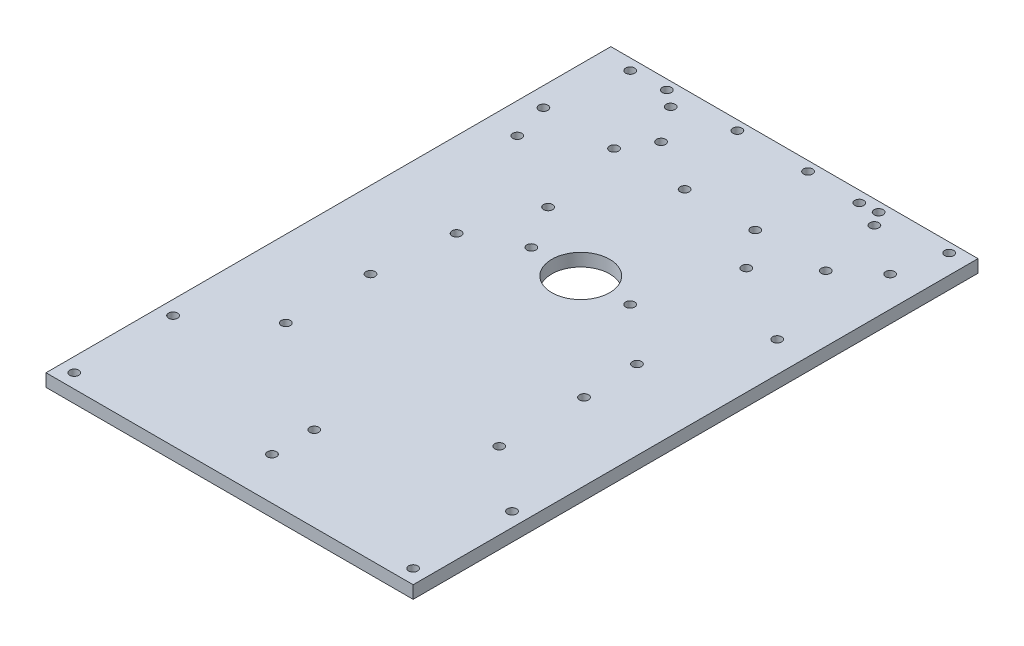
SolidWorks part; units mm, degrees
ref_plane "Front Plane" through (0, 0, 0) normal (0, 0, 1) x (1, 0, 0)
ref_plane "Top Plane" through (0, 0, 0) normal (0, 1, 0) x (1, 0, 0)
ref_plane "Right Plane" through (0, 0, 0) normal (1, 0, 0) x (0, 0, -1)
sketch "Sketch1" plane through (0, 0, 0) normal (0, 1, 0) x (1, 0, 0)
  line L0 (0, -55) -> (0, 55) construction
  line L5 (-65, -100) -> (65, -100)
  line L6 (-65, -100) -> (-65, 100)
  line L7 (-65, 100) -> (65, 100)
  line L8 (65, -100) -> (65, 100)
  line L9 (-65, -100) -> (65, 100) construction
  line L10 (-65, 100) -> (65, -100) construction
  line L11 (0, 100) -> (0, -100) construction
  line L12 (-100, -100) -> (100, -100) construction
  line L13 (-100, -100) -> (-100, 100) construction
  line L14 (-100, 100) -> (100, 100) construction
  line L15 (100, -100) -> (100, 100) construction
  line L16 (-100, -100) -> (100, 100) construction
  line L17 (-100, 100) -> (100, -100) construction
  point P0 (0, 0)
  point P1 (0, 0)
  point P6 (0, 0)
  dimension "D1" = 200
  dimension "D2" = 200
  dimension "D3" = 200
  dimension "D4" = 130
extrude "Boss-Extrude1" add sketch "Sketch1" along normal blind 4.5
sketch "Sketch3" plane through (0, 0, 0) normal (0, 1, 0) x (1, 0, 0)
  line L0 (-65, -90) -> (-55, -100) construction
  line L1 (-65, -100) -> (-55, -100) construction
  line L2 (-65, -100) -> (-65, -90) construction
  line L3 (-65, -90) -> (-55, -90) construction
  line L4 (-55, -100) -> (-55, -90) construction
  line L5 (-55, -90) -> (-65, -100) construction
  line L6 (0, -55) -> (0, 55) construction
  line L7 (65, -100) -> (55, -100) construction
  line L8 (65, -100) -> (65, -90) construction
  line L9 (65, -90) -> (55, -100) construction
  line L10 (65, -90) -> (55, -90) construction
  line L11 (55, -90) -> (65, -100) construction
  line L12 (55, -100) -> (55, -90) construction
  line L13 (-65, 100) -> (-65, -100) construction
  line L14 (-65, -65) -> (-55, -65) construction
  line L15 (-65, -65) -> (-65, -55) construction
  line L16 (-65, -55) -> (-55, -55) construction
  line L17 (-55, -65) -> (-55, -55) construction
  line L18 (-55, -55) -> (-65, -65) construction
  line L19 (-65, -65) -> (-55, -65) construction
  line L20 (-55, -65) -> (-65, -55) construction
  line L21 (55, -65) -> (65, -55) construction
  line L22 (65, -65) -> (55, -65) construction
  line L23 (55, -55) -> (65, -65) construction
  line L24 (55, -65) -> (55, -55) construction
  line L25 (65, -65) -> (65, -55) construction
  line L26 (65, -65) -> (55, -65) construction
  line L27 (65, -55) -> (55, -55) construction
  circle A0 centre (-60, -95) radius 1.6
  circle A1 centre (60, -95) radius 1.6
  circle A2 centre (-60, -60) radius 1.6
  circle A3 centre (60, -60) radius 1.6
  dimension "D3" = 3.2
  dimension "D7" = 3.2
  dimension "D1" = 10
  dimension "D2" = 10
  dimension "D4" = 10
  dimension "D5" = 10
  dimension "D6" = 25
extrude "Cut-Extrude1" cut sketch "Sketch3" along normal up to surface (4.5 mm away) up to face at (0, 4.5, 0)
sketch "Sketch4" plane through (0, 0, 0) normal (0, 1, 0) x (1, 0, 0)
  line L0 (42.545, 100) -> (-42.545, 100) construction
  line L1 (42.545, 100) -> (42.545, 1.702) construction
  line L2 (42.545, 1.702) -> (-42.545, 1.702) construction
  line L3 (-42.545, 100) -> (-42.545, 1.702) construction
  line L4 (42.545, 100) -> (-42.545, 1.702) construction
  line L5 (42.545, 1.702) -> (-42.545, 100) construction
  line L6 (0, 100) -> (0, 1.702) construction
  line L8 (0, -2.475) -> (0, 2.475) construction
  line L10 (42.545, 50.851) -> (-42.545, 50.851) construction
  line L12 (65, 100) -> (-65, 100) construction
  line L14 (65, -100) -> (65, 100)
  line L15 (65, 100) -> (-65, 100)
  line L16 (-65, 100) -> (-65, -100)
  line L17 (-65, -100) -> (65, -100)
  line L18 (65, -100) -> (65, 100)
  line L19 (65, 100) -> (-65, 100)
  line L20 (-65, 100) -> (-65, -100)
  line L21 (-65, -100) -> (65, -100)
  circle A0 centre (36.957, 7.29) radius 1.6
  circle A2 centre (-35.945, 92.13) radius 1.6
  circle A3 centre (36.445, 91.87) radius 1.6
  circle A4 centre (-35.055, 15.432) radius 1.6
  point P0 (0, 50.851)
  point P25 (0, 0)
  dimension "D3" = 0
  dimension "D4" = 3.2
  dimension "D5" = 13.73
  dimension "D1" = 85.09
  dimension "D2" = 98.298
  dimension "D6" = 5.588
  dimension "D7" = 5.588
  dimension "D8" = 6.1
  dimension "D9" = 8.13
  dimension "D10" = 7.87
  dimension "D11" = 6.6
  dimension "D12" = 98.298
  dimension "D13" = 85.09
  dimension "D14" = 7.49
extrude "Cut-Extrude2" cut sketch "Sketch4" along normal up to surface (4.5 mm away) contours A4 | A0 | A3 | A2 up to face at (60, 4.5, 93.4)
sketch "Sketch5" plane through (0, 0, 0) normal (0, 1, 0) x (1, 0, 0)
  line L5 (32.8, -52.298) -> (32.8, -2.298) construction
  line L8 (42.8, -2.298) -> (42.8, -52.298) construction
  line L12 (-65, 1.702) -> (65, 1.702) construction
  line L14 (42.8, -2.298) -> (32.8, -2.298) construction
  line L15 (42.8, -52.298) -> (32.8, -52.298) construction
  line L18 (0, -2.475) -> (0, 2.475) construction
  line L19 (-42.8, -52.298) -> (-32.8, -52.298) construction
  line L20 (-42.8, -2.298) -> (-32.8, -2.298) construction
  line L21 (-42.8, -2.298) -> (-42.8, -52.298) construction
  line L22 (-32.8, -52.298) -> (-32.8, -2.298) construction
  circle A8 centre (37.8, -12.298) radius 1.6
  circle A9 centre (37.8, -42.298) radius 1.6
  circle A10 centre (-37.8, -42.298) radius 1.6
  circle A11 centre (-37.8, -12.298) radius 1.6
  dimension "D1" = 3.2
  dimension "D2" = 10
  dimension "D3" = 50
  dimension "D4" = 10
  dimension "D5" = 30
  dimension "D6" = 5
  dimension "D8" = 4
  dimension "D9" = 32.8
extrude "Cut-Extrude3" cut sketch "Sketch5" along normal up to surface (4.5 mm away) up to face at (-35.945, 4.5, -93.73)
sketch "Sketch6" plane through (0, 0, 0) normal (0, 1, 0) x (1, 0, 0)
  line L0 (18.522, 87.8715) -> (18.522, 100) construction
  line L1 (24.872, 75.743) -> (58.4, 75.743) construction
  line L2 (24.872, 75.743) -> (24.872, 100) construction
  line L3 (24.872, 100) -> (58.4, 100) construction
  line L4 (58.4, 75.743) -> (58.4, 100) construction
  line L5 (24.872, 75.743) -> (58.4, 100) construction
  line L6 (24.872, 100) -> (58.4, 75.743) construction
  line L7 (18.522, 82.7915) -> (18.522, 92.9515) construction
  line L8 (18.522, 92.9515) -> (24.872, 100) construction
  line L9 (18.522, 82.7915) -> (24.872, 75.743) construction
  line L10 (18.522, 87.8715) -> (58.4, 87.8715) construction
  line L11 (65, -100) -> (65, 100) construction
  line L12 (65, 100) -> (-65, 100) construction
  line L13 (24.872, 35.743) -> (58.4, 35.743) construction
  line L14 (58.4, 35.743) -> (58.4, 60) construction
  line L15 (24.872, 60) -> (58.4, 60) construction
  line L16 (18.522, 52.9515) -> (24.872, 60) construction
  line L17 (18.522, 42.7915) -> (18.522, 52.9515) construction
  line L18 (18.522, 42.7915) -> (24.872, 35.743) construction
  line L19 (24.872, 35.743) -> (58.4, 60) construction
  line L20 (18.522, 47.8715) -> (58.4, 47.8715) construction
  line L21 (24.872, 60) -> (58.4, 35.743) construction
  line L22 (0, -2.475) -> (0, 2.475) construction
  line L23 (-65, 100) -> (-65, -100) construction
  line L24 (-24.872, 60) -> (-58.4, 60) construction
  line L25 (-58.4, 60) -> (-58.4, 35.743) construction
  line L26 (-18.522, 87.8715) -> (-58.4, 87.8715) construction
  line L27 (-24.872, 35.743) -> (-58.4, 35.743) construction
  line L28 (-18.522, 42.7915) -> (-24.872, 35.743) construction
  line L29 (-18.522, 52.9515) -> (-18.522, 42.7915) construction
  line L30 (-18.522, 52.9515) -> (-24.872, 60) construction
  line L44 (-18.522, 87.8715) -> (-13.8994, 76.6585) construction
  line L45 (-24.872, 100) -> (-24.872, 75.743) construction
  line L46 (-24.872, 100) -> (-58.4, 75.743) construction
  line L47 (-24.872, 75.743) -> (-58.4, 100) construction
  line L48 (-24.872, 100) -> (-58.4, 100) construction
  line L49 (-24.872, 75.743) -> (-58.4, 75.743) construction
  line L50 (-58.4, 100) -> (-58.4, 75.743) construction
  line L51 (-18.522, 92.9515) -> (-18.522, 82.7915) construction
  line L52 (-18.522, 82.7915) -> (-24.872, 75.743) construction
  line L53 (-18.522, 92.9515) -> (-24.872, 100) construction
  circle A0 centre (54.21, 79.68) radius 1.6
  circle A1 centre (26.904, 96.063) radius 1.6
  circle A2 centre (26.904, 56.063) radius 1.6
  circle A3 centre (54.21, 39.68) radius 1.6
  circle A8 centre (-54.21, 96.063) radius 1.6
  circle A9 centre (-26.904, 79.68) radius 1.6
  circle A10 centre (-54.21, 56.063) radius 1.6
  circle A11 centre (-26.904, 39.68) radius 1.6
  point P0 (41.636, 87.8715)
  point P10 (18.522, 87.8715)
  point P58 (-18.522, 87.8715)
  point P59 (-41.636, 87.8715)
  dimension "D5" = 3.2
  dimension "D6" = 3.2
  dimension "D26" = 3.2
  dimension "D28" = 3.2
  dimension "D1" = 33.528
  dimension "D2" = 24.257
  dimension "D3" = 39.878
  dimension "D4" = 10.16
  dimension "D7" = 4.19
  dimension "D8" = 3.937
  dimension "D9" = 3.937
  dimension "D10" = 2.032
  dimension "D11" = 6.6
  dimension "D13" = 40
  dimension "D14" = 33.528
  dimension "D15" = 39.878
  dimension "D16" = 24.257
  dimension "D17" = 10.16
  dimension "D18" = 3.937
  dimension "D19" = 2.032
  dimension "D20" = 4.19
  dimension "D21" = 3.937
  dimension "D22" = 6.6
  dimension "D23" = 9.487
  dimension "D24" = 9.487
  dimension "D25" = 33.528
  dimension "D27" = 12.1285
  dimension "D30" = 40
  dimension "D12" = 2
  dimension "D29" = 2
extrude "Cut-Extrude4" cut sketch "Sketch6" along normal up to surface (4.5 mm away) up to face at (37.8, 4.5, 40.698)
sketch "Sketch7" plane through (0, 0, 0) normal (0, 1, 0) x (1, 0, 0)
  line L0 (0, 105) -> (11.2943, 105) construction
  line L1 (-12.1285, 98.65) -> (-12.1285, 65.122) construction
  line L2 (-12.1285, 98.65) -> (12.1285, 98.65) construction
  line L3 (12.1285, 98.65) -> (12.1285, 65.122) construction
  line L4 (-12.1285, 65.122) -> (12.1285, 65.122) construction
  line L5 (-12.1285, 98.65) -> (12.1285, 65.122) construction
  line L6 (12.1285, 98.65) -> (-12.1285, 65.122) construction
  line L7 (-5.08, 105) -> (5.08, 105) construction
  line L8 (5.08, 105) -> (12.1285, 98.65) construction
  line L9 (-5.08, 105) -> (-12.1285, 98.65) construction
  line L10 (0, 105) -> (0, 65.122) construction
  line L11 (25, 105) -> (36.2943, 105) construction
  line L12 (12.1285, 85.061) -> (-12.1285, 85.061) construction
  line L13 (0, -2.475) -> (0, 2.475) construction
  line L14 (65, 100) -> (-65, 100) construction
  line L15 (12.8715, 98.65) -> (12.8715, 65.122) construction
  line L16 (12.8715, 98.65) -> (37.1285, 98.65) construction
  line L17 (37.1285, 98.65) -> (37.1285, 65.122) construction
  line L18 (12.8715, 65.122) -> (37.1285, 65.122) construction
  line L19 (12.8715, 98.65) -> (37.1285, 65.122) construction
  line L20 (37.1285, 98.65) -> (12.8715, 65.122) construction
  line L21 (19.92, 105) -> (30.08, 105) construction
  line L22 (30.08, 105) -> (37.1285, 98.65) construction
  line L23 (19.92, 105) -> (12.8715, 98.65) construction
  line L24 (25, 105) -> (25, 65.122) construction
  line L25 (37.1285, 85.061) -> (12.8715, 85.061) construction
  line L26 (50, 105) -> (61.2943, 105) construction
  line L27 (37.8715, 98.65) -> (37.8715, 65.122) construction
  line L28 (37.8715, 98.65) -> (62.1285, 98.65) construction
  line L29 (62.1285, 98.65) -> (62.1285, 65.122) construction
  line L30 (37.8715, 65.122) -> (62.1285, 65.122) construction
  line L31 (37.8715, 98.65) -> (62.1285, 65.122) construction
  line L32 (62.1285, 98.65) -> (37.8715, 65.122) construction
  line L33 (44.92, 105) -> (55.08, 105) construction
  line L34 (55.08, 105) -> (62.1285, 98.65) construction
  line L35 (44.92, 105) -> (37.8715, 98.65) construction
  line L36 (50, 105) -> (50, 65.122) construction
  line L37 (62.1285, 85.061) -> (37.8715, 85.061) construction
  line L38 (0, 105) -> (25, 105) construction
  line L39 (-25, 105) -> (-13.7057, 105) construction
  line L40 (-37.1285, 98.65) -> (-37.1285, 65.122) construction
  line L41 (-37.1285, 98.65) -> (-12.8715, 98.65) construction
  line L42 (-37.1285, 65.122) -> (-12.8715, 65.122) construction
  line L43 (-37.1285, 98.65) -> (-12.8715, 65.122) construction
  line L44 (-12.8715, 98.65) -> (-37.1285, 65.122) construction
  line L45 (-30.08, 105) -> (-19.92, 105) construction
  line L46 (-19.92, 105) -> (-12.8715, 98.65) construction
  line L47 (-30.08, 105) -> (-37.1285, 98.65) construction
  line L48 (-25, 105) -> (-25, 65.122) construction
  line L49 (-12.8715, 85.061) -> (-37.1285, 85.061) construction
  line L50 (-12.8715, 98.65) -> (-12.8715, 65.122) construction
  line L51 (-50, 105) -> (-38.7057, 105) construction
  line L52 (-62.1285, 98.65) -> (-62.1285, 65.122) construction
  line L53 (-62.1285, 98.65) -> (-37.8715, 98.65) construction
  line L54 (-62.1285, 65.122) -> (-37.8715, 65.122) construction
  line L55 (-62.1285, 98.65) -> (-37.8715, 65.122) construction
  line L56 (-37.8715, 98.65) -> (-62.1285, 65.122) construction
  line L57 (-55.08, 105) -> (-44.92, 105) construction
  line L58 (-44.92, 105) -> (-37.8715, 98.65) construction
  line L59 (-55.08, 105) -> (-62.1285, 98.65) construction
  line L60 (-50, 105) -> (-50, 65.122) construction
  line L61 (-37.8715, 85.061) -> (-62.1285, 85.061) construction
  line L62 (-37.8715, 98.65) -> (-37.8715, 65.122) construction
  line L63 (0, 105) -> (-25, 105) construction
  circle A0 centre (-8.1915, 69.312) radius 1.6
  circle A1 centre (8.1915, 96.618) radius 1.6
  circle A2 centre (16.8085, 69.312) radius 1.6
  circle A3 centre (33.1915, 96.618) radius 1.6
  circle A4 centre (41.8085, 69.312) radius 1.6
  circle A5 centre (58.1915, 96.618) radius 1.6
  circle A6 centre (-33.1915, 69.312) radius 1.6
  circle A7 centre (-16.8085, 96.618) radius 1.6
  circle A8 centre (-58.1915, 69.312) radius 1.6
  circle A9 centre (-41.8085, 96.618) radius 1.6
  point P0 (0, 81.886)
  point P10 (0, 105)
  point P23 (25, 81.886)
  point P33 (25, 105)
  point P40 (50, 81.886)
  point P50 (50, 105)
  point P59 (-25, 81.886)
  point P69 (-25, 105)
  point P76 (-50, 81.886)
  point P86 (-50, 105)
  dimension "D5" = 3.2
  dimension "D6" = 3.2
  dimension "D1" = 33.528
  dimension "D2" = 24.257
  dimension "D3" = 39.878
  dimension "D4" = 10.16
  dimension "D7" = 4.19
  dimension "D8" = 3.937
  dimension "D9" = 3.937
  dimension "D10" = 2.032
  dimension "D11" = 6.35
  dimension "D12" = 19.939
  dimension "D13" = 5
  dimension "D15" = 25
  dimension "D17" = 25
  dimension "D14" = 3
  dimension "D16" = 3
extrude "Cut-Extrude5" cut sketch "Sketch7" along normal up to surface (4.5 mm away) up to face at (-54.21, 4.5, -57.663)
sketch "Sketch9" plane through (0, 0, 0) normal (0, 1, 0) x (1, 0, 0)
  circle A1 centre (0, -70) radius 1.6
  circle A2 centre (0, -70) radius 1.6
  circle A3 centre (0, -85) radius 1.6
  circle A4 centre (0, -85) radius 1.6
  circle A5 centre (17.5, 24.3455) radius 1.6
  circle A6 centre (0, 24.3455) radius 10.25
  circle A7 centre (0, 24.3455) radius 10.25
  circle A10 centre (17.5, 24.3455) radius 1.6
  circle A11 centre (-17.5, 24.3455) radius 1.6
  circle A12 centre (-17.5, 24.3455) radius 1.6
  dimension "D1" = 0
  dimension "D2" = 0
  dimension "D3" = 0
  dimension "D4" = 0
  dimension "D5" = 0
extrude "Cut-Extrude6" cut sketch "Sketch9" along normal up to surface (4.5 mm away) up to face at (58.1915, 4.5, -98.218)
